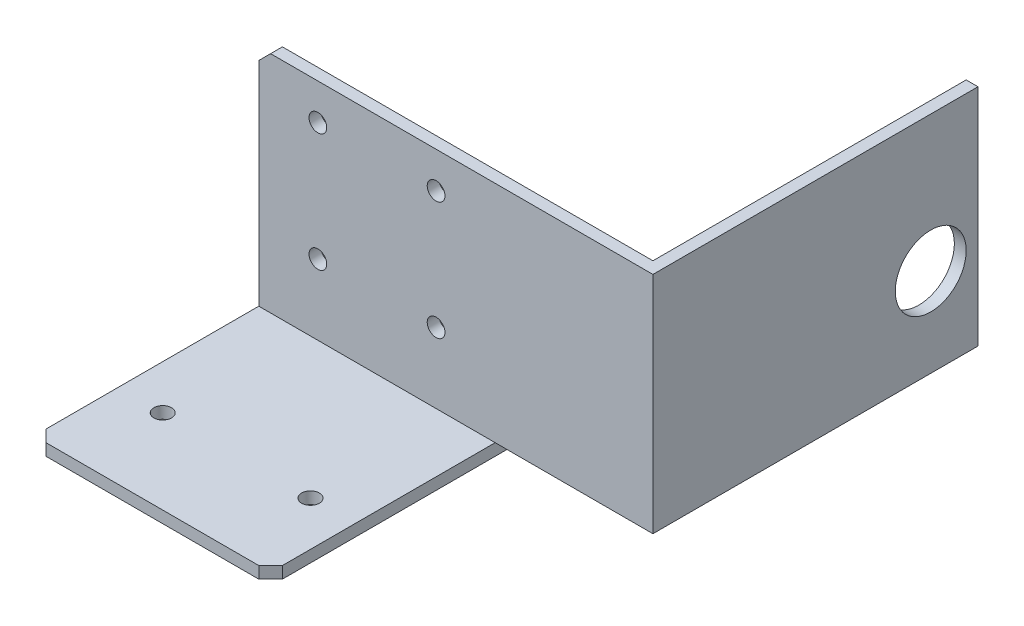
SolidWorks part; units mm, degrees
ref_plane "Спереди" through (0, 0, 0) normal (0, 0, 1) x (1, 0, 0)
ref_plane "Сверху" through (0, 0, 0) normal (0, 1, 0) x (1, 0, 0)
ref_plane "Справа" through (0, 0, 0) normal (1, 0, 0) x (0, 0, -1)
sketch "Sketch1" plane through (0, 0, 0) normal (1, 0, 0) x (0, 0, -1)
  line L0 (0, 0) -> (0, 38)
  line L1 (0, 38) -> (2, 38)
  line L2 (2, 38) -> (2, -2)
  line L3 (2, -2) -> (-38, -2)
  line L4 (-38, -2) -> (-38, 0)
  line L5 (-38, 0) -> (0, 0)
  dimension "D1" = 2
  dimension "D2" = 2
  dimension "D3" = 40
  dimension "D4" = 40
extrude "Extrude1" add sketch "Sketch1" along normal blind 40
sketch "Sketch2" plane through (0, -2, 0) normal (0, -1, 0) x (-1, 0, 0)
  line L0 (-40, 2) -> (0, 2) construction
  line L1 (-7.5, -23.75) -> (-32.5, -23.75) construction
  line L2 (-40, -38) -> (0, -38) construction
  circle A0 centre (-32.5, -23.75) radius 1.5
  circle A1 centre (-7.5, -23.75) radius 1.5
  point P5 (-20, -23.75)
  point P10 (-20, -38)
  dimension "D1" = 3
  dimension "D2" = 25
  dimension "D3" = 25.75
extrude "Extrude2" cut sketch "Sketch2" against normal up to next contours A0
sketch "Sketch3" plane through (0, 0, -2) normal (0, 0, -1) x (-1, 0, 0)
  line L1 (0, -2) -> (0, 38) construction
  line L2 (-40, 38) -> (0, 38) construction
  circle A0 centre (-10, 31.9) radius 1.5
  circle A1 centre (-30, 31.9) radius 1.5
  circle A2 centre (-30, 11.9) radius 1.5
  circle A3 centre (-10, 11.9) radius 1.5
  dimension "D1" = 10
  dimension "D2" = 6.1
  dimension "D3" = 2
  dimension "D4" = 2
extrude "Extrude3" cut sketch "Sketch3" against normal up to next
chamfer "Chamfer1" distance 2 angle 45 4 edges at (40, -1, 38) (0, -1, 38) (0, 38, -1) (40, 38, -1)
sketch "Sketch4" plane through (40, 0, 0) normal (1, 0, 0) x (0, 0, -1)
  line L0 (0, 36) -> (0, 38) construction
  line L1 (0, 38) -> (2, 38)
  line L2 (0, 38) -> (0, 0)
  line L3 (0, 0) -> (2, 0)
  line L4 (2, 38) -> (2, 0)
  line L5 (2, -2) -> (2, 36) construction
  line L6 (0, 38) -> (2, 38) construction
extrude "Boss-Extrude1" add sketch "Sketch4" along normal blind 26.69 and the other way blind 3
sketch "Sketch5" plane through (66.69, 0, 0) normal (1, 0, 0) x (0, 0, -1)
  line L0 (2, 0) -> (2, 38) construction
  line L1 (2, 38) -> (55, 38)
  line L2 (2, 38) -> (2, 0)
  line L3 (2, 0) -> (55, 0)
  line L4 (55, 38) -> (55, 0)
  line L5 (2, 38) -> (0, 38) construction
  line L6 (0, 0) -> (2, 0) construction
  dimension "D1" = 53
extrude "Boss-Extrude2" add sketch "Sketch5" against normal blind 2
sketch "Sketch6" plane through (66.69, 0, 0) normal (1, 0, 0) x (0, 0, -1)
  line L1 (0, 0) -> (55, 0) construction
  line L2 (2, -2) -> (2, 0) construction
  circle A0 centre (47, 15) radius 6
  dimension "D1" = 12
  dimension "D2" = 45
  dimension "D3" = 15
extrude "Cut-Extrude1" cut sketch "Sketch6" against normal blind 3
